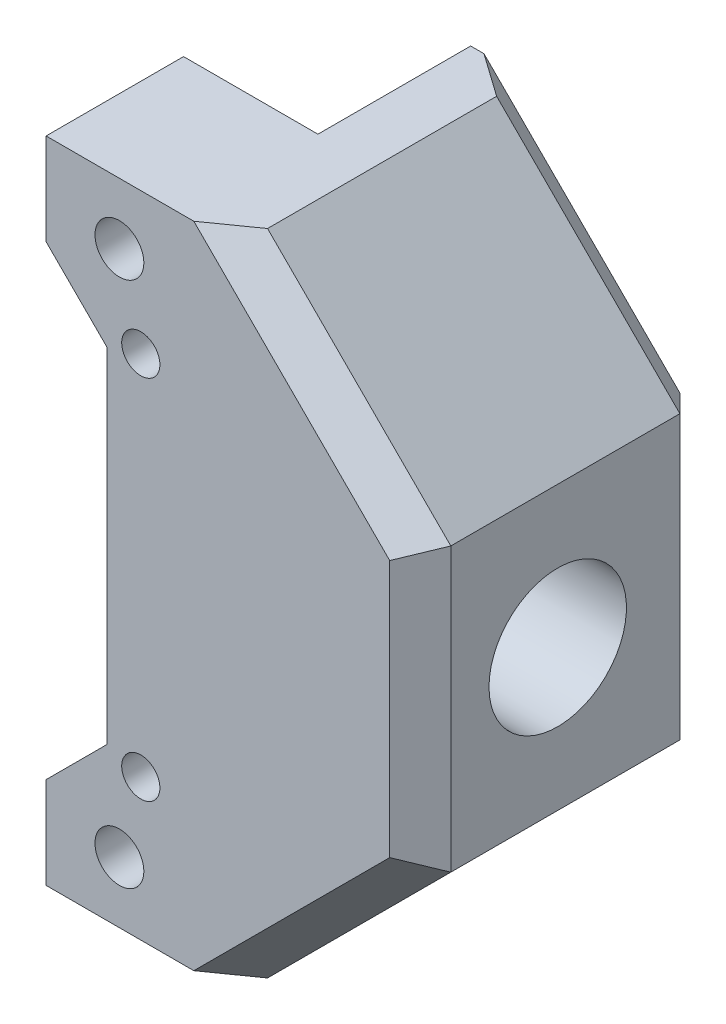
SolidWorks part; units mm, degrees
ref_plane "Plan de face" through (0, 0, 0) normal (0, 0, 1) x (1, 0, 0)
ref_plane "Plan de dessus" through (0, 0, 0) normal (0, 1, 0) x (1, 0, 0)
ref_plane "Plan de droite" through (0, 0, 0) normal (1, 0, 0) x (0, 0, -1)
sketch "Esquisse1" plane through (0, 0, 0) normal (0, 0, 1) x (1, 0, 0)
  line L0 (38.6155, 27.25) -> (38.6155, 15.25)
  line L1 (33.8155, 15.25) -> (33.8155, 27.25)
  line L6 (33.8155, 15.25) -> (33.8155, 10)
  line L7 (33.8155, 10) -> (29.8155, 6)
  line L8 (29.8155, 6) -> (29.8155, 0)
  line L9 (29.8155, 0) -> (38.6155, 0)
  line L10 (38.6155, 0) -> (38.6155, 15.25)
  line L11 (38.6155, 15.25) -> (33.8155, 15.25)
  line L12 (33.8155, 15.25) -> (33.8155, 10)
  line L13 (33.8155, 10) -> (29.8155, 6)
  line L14 (29.8155, 6) -> (29.8155, 0)
  line L15 (29.8155, 0) -> (38.6155, 0)
  line L16 (38.6155, 0) -> (38.6155, 15.25)
  line L18 (29.8155, 42.5) -> (29.8155, 36.5)
  line L19 (29.8155, 36.5) -> (33.8155, 32.5)
  line L20 (33.8155, 32.5) -> (33.8155, 27.25)
  line L21 (33.8155, 27.25) -> (38.6155, 27.25)
  line L22 (38.6155, 27.25) -> (38.6155, 42.5)
  line L23 (38.6155, 42.5) -> (29.8155, 42.5)
  line L24 (29.8155, 42.5) -> (29.8155, 36.5)
  line L25 (29.8155, 36.5) -> (33.8155, 32.5)
  line L26 (33.8155, 32.5) -> (33.8155, 27.25)
  line L28 (38.6155, 27.25) -> (38.6155, 42.5)
  line L29 (38.6155, 42.5) -> (29.8155, 42.5)
  circle A0 centre (34.6155, 4) radius 1.6 construction
  circle A1 centre (34.6155, 4) radius 1.6
  circle A2 centre (34.6155, 38.5) radius 1.6 construction
  circle A3 centre (34.6155, 38.5) radius 1.6
  dimension "D1" = 0
  dimension "D2" = 0
extrude "Boss.-Extru.1" add sketch "Esquisse1" along normal blind 9
sketch "Esquisse2" plane through (0, 0, 9) normal (0, 0, 1) x (1, 0, 0)
  line L0 (38.6155, 0) -> (54.3155, 0)
  line L1 (54.3155, 0) -> (54.3155, 42.5)
  line L2 (54.3155, 42.5) -> (38.6155, 42.5)
  line L3 (38.6155, 42.5) -> (38.6155, 0)
  line L4 (46.3155, 17.25) -> (46.3155, 25.25) construction
  dimension "D1" = 8
extrude "Boss.-Extru.2" add sketch "Esquisse2" against normal up to surface (19 mm away)
sketch "Esquisse4" plane through (33.8155, 0, 0) normal (-1, 0, 0) x (0, 0, 1)
  line L0 (0, 32.5) -> (0, 10) construction
  circle A0 centre (0, 21.25) radius 6
  dimension "D1" = 12
extrude "Enlèv. mat.-Extru.1" cut sketch "Esquisse4" against normal up to surface (4.8 mm away) up to face at (38.6155, 15.9375, -7.5)
sketch "Esquisse5" plane through (38.6155, 0, 0) normal (-1, 0, 0) x (0, 0, 1)
  line L0 (0, 29.25) -> (-10, 29.25)
  line L1 (-10, 0) -> (-10, 42.5) construction
  line L2 (0, 13.25) -> (-10, 13.25)
  line L3 (-10, 13.25) -> (-10, 29.25)
  arc A0 (0, 13.25) -> (0, 29.25) centre (0, 21.25) ccw
  dimension "D1" = 16
extrude "Enlèv. mat.-Extru.2" cut sketch "Esquisse5" against normal blind 5
sketch "Esquisse6" plane through (43.6155, 0, 0) normal (-1, 0, 0) x (0, 0, 1)
  circle A0 centre (0, 21.25) radius 4.5
  dimension "D1" = 9
extrude "Enlèv. mat.-Extru.3" cut sketch "Esquisse6" against normal through all
chamfer "Chanfrein1" distance 12 angle 45 2 edges at (54.3155, 42.5, -0.5) (54.3155, 0, -0.5)
chamfer "Chanfrein2" distance 2 angle 45 6 edges at (48.3155, 36.5, -10) (54.3155, 21.25, -10) (48.3155, 6, -10) (48.3155, 36.5, 9) (54.3155, 21.25, 9) (48.3155, 6, 9)
hole_wizard "Trou pour taraudage pour trou taraudé M31" positions "Esquisse8" profile "Esquisse7" hole size "M3" standard "Din" end condition through all
sketch "Esquisse8" plane through (0, 0, 9) normal (0, 0, 1) x (1, 0, 0)
  line L0 (36.0155, 9.25) -> (36.0155, 33.25) construction
  line L1 (36.0155, 21.25) -> (33.8155, 21.25) construction
  line L2 (33.8155, 32.5) -> (33.8155, 10) construction
  point P0 (36.0155, 33.25)
  point P2 (36.0155, 9.25)
  dimension "D1" = 24
  dimension "D2" = 2.2
sketch "Esquisse7" plane through (36.0155, 33.25, 9) normal (1, 0, 0) x (0, -1, 0)
  line L0 (0, 0) -> (0, 19)
  line L1 (0, 19) -> (1.25, 19)
  line L2 (1.25, 19) -> (1.25, 0)
  line L5 (1.25, 0) -> (0, 0)
  line L11 (0, -6.35) -> (0, 107.95) construction
  dimension "Diamètre du perçage jusqu'au prochain" = 2.5
  dimension "Profondeur du perçage jusqu'au prochain" = 19
